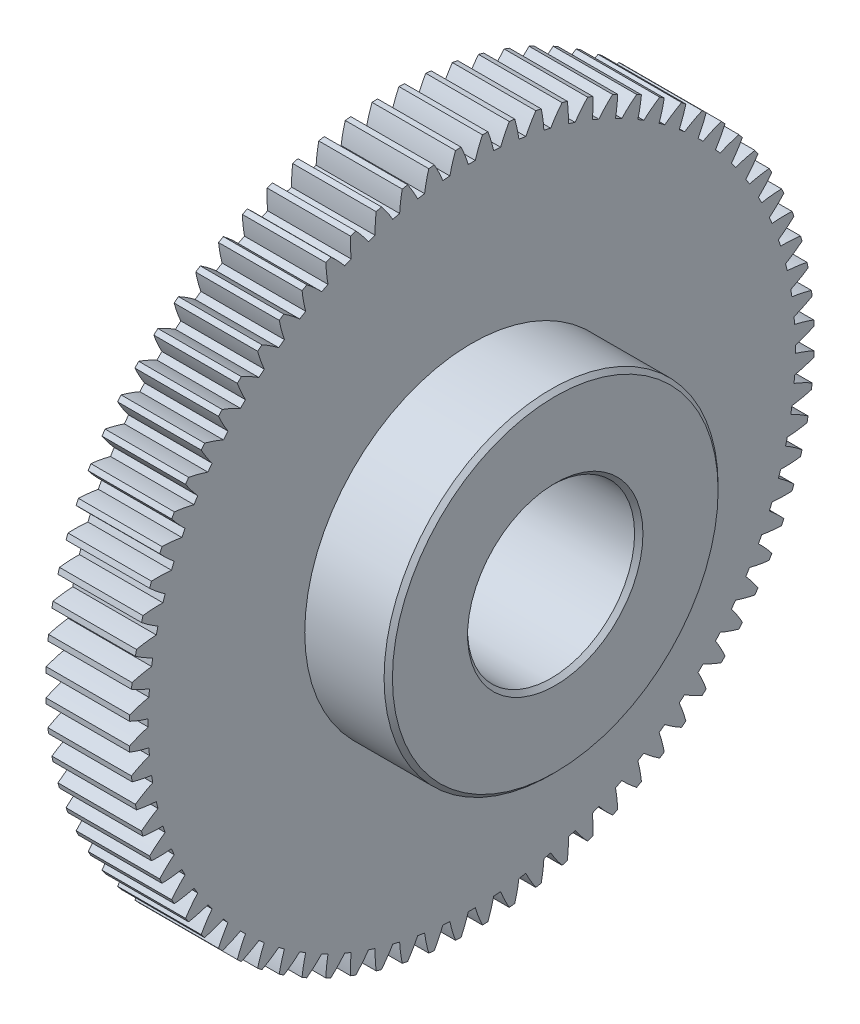
SolidWorks part; units mm, degrees
material "AISI 1045 鋼，冷拉"
ref_plane "Plane1" through (0, 0, 0) normal (0, 0, 1) x (1, 0, 0)
ref_plane "Plane2" through (0, 0, 0) normal (0, 1, 0) x (1, 0, 0)
ref_plane "Plane3" through (0, 0, 0) normal (1, 0, 0) x (0, 0, -1)
sketch "HoldingSke" plane through (0, 0, 0) normal (0, 1, 0) x (1, 0, 0)
  line L0 (0, 0) -> (0.1736, -0.9848)
  line L1 (-15, 0) -> (100, 0) construction
  line L2 (0, 0) -> (-2.1039, 2.3779)
  line L3 (0, 0) -> (-11.863, 4.5341)
  line L4 (0, 0) -> (1.4996, 8.5048)
  line L5 (0, 0) -> (-46.8476, -17.4728)
  line L6 (0, 0) -> (-8.2896, -5.593)
  line L7 (-2.1039, 2.3779) -> (8.6586, 51.2059)
  line L8 (-76.2, 54.61) -> (-76.1, 54.61)
  line L9 (-71.009, 38.7566) -> (-53.1078, 45.2721)
  line L10 (-76.2, 71.12) -> (104.1128, 71.12)
  line L11 (0, 0) -> (-10, 0)
  line L12 (-76.2, 101.6) -> (-76.162, 101.6)
  line L13 (24.9733, 27.94) -> (52.9518, 28.4284)
  line L14 (24.9733, 27.94) -> (24.9743, 27.94)
  line L15 (24.9733, 27.94) -> (100.4006, 29.5858)
  line L16 (-63.627, -1) -> (-12.827, -1)
  circle A0 centre (0, 0) radius 0.4
  circle A1 centre (0, 0) radius 37.5
  circle A2 centre (0, 0) radius 37.5
  circle A3 centre (0, 0) radius 0.4
  dimension "MHD" = 75
  dimension "Hub_dia" = 75
  dimension "Bore" = 0.8
  dimension "MBD" = 0.8
  dimension "Num_teeth" = 80
  dimension "Pitch" = 1
  dimension "Overall_len" = 50
  dimension "Show_teeth" = 80
  dimension "Thickness" = 10
  dimension "OAL" = 50.0001
  dimension "T_dim" = 0.1
  dimension "Ap" = 20
  dimension "H" = 19.05
  dimension "Pitch_radius" = 180.3128
  dimension "Width" = 10
  dimension "Backlash" = 0.038
  dimension "Addendum_fac" = 1
  dimension "Dedendum_fac" = 1.25
  dimension "Clearance_fac" = 0.25
  dimension "Dedendum_add" = 0.001
  dimension "Module" = 1
sketch "BasProSke" plane through (0, 0, 0) normal (0, 1, 0) x (1, 0, 0)
  line L0 (-10, 0) -> (60, 0) construction
  line L1 (0, 0) -> (0, 41)
  line L2 (0, 0) -> (10, 0)
  line L3 (10, 0) -> (10, 41)
  line L4 (10, 41) -> (0, 41)
  dimension "Thickness" = 10
  dimension "Diameter" = 82
revolve "Base-Revolve" add sketch "BasProSke" angle 360 about L0
sketch "TooCutSke" plane through (0, 0, 0) normal (1, 0, 0) x (0, 0, -1)
  line L1 (0, 0) -> (0, 107) construction
  line L2 (0, 0) -> (-0.8518, 39.9909) construction
  line L3 (0, 0) -> (-3.1403, 79.9254) construction
  line L4 (-0.8518, 39.9909) -> (-1.5701, 39.9627) construction
  arc A0 (0.4206, 38.7467) -> (-0.4206, 38.7467) centre (0, 0) ccw
  arc A1 (1.2919, 41.0051) -> (-1.2919, 41.0051) centre (0, 0) ccw
  circle A2 centre (0, 0) radius 40 construction
  circle A3 centre (0, 0) radius 37.5877 construction
  arc A4 (-0.4206, 38.7467) -> (-1.2919, 41.0051) centre (-15.7409, 34.133) ccw
  arc A5 (1.2919, 41.0051) -> (0.4206, 38.7467) centre (15.7409, 34.133) ccw
  dimension "Root_dia" = 77.498
  dimension "Overcut_dia" = 82.0508
  dimension "Pitch_dia" = 80
  dimension "Base_dia" = 75.1754
  dimension "Flank_rad" = 16
  dimension "Half_ang" = 2.25
  dimension "Half_CT" = 0.7188
extrude "ToothCut" cut sketch "TooCutSke" along normal through all
fillet "Breaks" [suppressed] radius 0.02
fillet "RootFillets" [suppressed] radius 0.251
pattern_circular "TeethCuts" count 80 every 4.5 about axis through (-10, 0, 0) along (1, 0, 0) of "ToothCut", "Breaks", "RootFillets"
sketch "HubNeaOneSke" plane through (0, 0, 0) normal (-1, 0, 0) x (0, 0, 1)
  circle A0 centre (0, 0) radius 37.5
  dimension "Diameter" = 75
extrude "HubNearOne" [suppressed] add sketch "HubNeaOneSke" along normal blind 40.0001
sketch "HubNeaBotSke" plane through (0, 0, 0) normal (-1, 0, 0) x (0, 0, 1)
  circle A0 centre (0, 0) radius 37.5
  dimension "Diameter" = 75
extrude "HubNearBoth" [suppressed] add sketch "HubNeaBotSke" along normal blind 20
ref_plane "FarPln" through (10, 0, 0) normal (1, 0, 0) x (0, 0, -1)
sketch "HubFarSke" plane through (10, 0, 0) normal (1, 0, 0) x (0, 0, -1)
  circle A0 centre (0, 0) radius 37.5
  dimension "Diameter" = 75
extrude "HubFar" [suppressed] add sketch "HubFarSke" along normal blind 20
sketch "草圖1" plane through (10, 0, 0) normal (1, 0, 0) x (0, 0, -1)
  circle A0 centre (0, 0) radius 20
  dimension "D1" = 40
extrude "填料-伸長1" add sketch "草圖1" along normal blind 10
sketch "BorSke" plane through (0, 0, 0) normal (1, 0, 0) x (0, 0, -1)
  circle A0 centre (0, 0) radius 10
  dimension "Diameter" = 20
extrude "Bore" cut sketch "BorSke" along normal mid plane 100.0001
sketch "KeySke" plane through (0, 0, 0) normal (1, 0, 0) x (0, 0, -1)
  line L0 (-0.05, 0) -> (-0.05, 0.5)
  line L1 (-0.05, 0.5) -> (0.05, 0.5)
  line L2 (0.05, 0.5) -> (0.05, 0)
  line L3 (0, 0) -> (0, 34) construction
  line L4 (-0.05, 0) -> (0.05, 0)
  dimension "Offset" = 0.5
  dimension "Width" = 0.1
extrude "Keyway" [suppressed] cut sketch "KeySke" along normal mid plane 100.0001
pattern_circular "Keyway2" [suppressed] count 2 every 90 about axis through (-10, 0, 0) along (1, 0, 0)
chamfer "導角1" distance 0.5 angle 45 3 edges at (0, 0, -10) (20, 0, -10) (20, 0, -20)
equation "' \"Module@HoldingSke\" = 6.35"
equation "' \"Num_teeth@HoldingSke\" = 12"
equation "' \"Ap@HoldingSke\" =  20"
equation "' \"Ap@HoldingSke\" = 20"
equation "' \"Width@HoldingSke\" = 0.5 * 25.4"
equation "' \"Hub_dia@HoldingSke\"= 1 * 25.4"
equation "' \"Hub_dia@HoldingSke\" = 1 * 25.4"
equation "' \"Overall_len@HoldingSke\" = 1.0 * 25.4"
equation "' \"Bore@HoldingSke\" = 0.75 * 25.4"
equation "' \"T_dim@HoldingSke\" = 0.1 * 25.4"
equation "' \"Width@KeySke\" = 0.25 * 25.4"
equation "' \"Show_teeth@HoldingSke\" = 13"
equation "' \"Backlash@HoldingSke\" = 0.009 * 25.4"
equation "' \"Addendum_fac@HoldingSke\" = 1.0"
equation "' \"Dedendum_fac@HoldingSke\" = 1.25"
equation "' \"Dedendum_add@HoldingSke\" = 0.00005 * 25.4"
equation "' \"Clearance_fac@HoldingSke\" = 0.25"
equation "\"Pitch@HoldingSke\" = 1 / \"Module@HoldingSke\""
equation "\"Overcut_dia@TooCutSke\" = (\"Num_teeth@HoldingSke\" + 2 * \"Addendum_fac@HoldingSke\") / \"Pitch@HoldingSke\" + 0.002 * 25.4"
equation "\"Pitch_dia@TooCutSke\" = \"Num_teeth@HoldingSke\" / \"Pitch@HoldingSke\""
equation "\"Base_dia@TooCutSke\" = \"Num_teeth@HoldingSke\" / \"Pitch@HoldingSke\" * cos((\"Ap@HoldingSke\"  * 3.14159265 / 180))"
equation "\"Root_dia@TooCutSke\" = (\"Num_teeth@HoldingSke\" + 2) / \"Pitch@HoldingSke\" - 2 * (\"Addendum_fac@HoldingSke\" + \"Dedendum_fac@HoldingSke\") / \"Pitch@HoldingSke\" - \"Dedendum_add@HoldingSke\" * 2"
equation "\"Half_ang@TooCutSke\" = 180 / \"Num_teeth@HoldingSke\""
equation "\"Half_CT@TooCutSke\" = \"Num_teeth@HoldingSke\" / \"Pitch@HoldingSke\" * sin((3.14159265 / 2 / \"Num_teeth@HoldingSke\")) / 2 - 7 * \"Backlash@HoldingSke\" / 4"
equation "\"Flank_rad@TooCutSke\" = \"Num_teeth@HoldingSke\" / \"Pitch@HoldingSke\" / 5"
equation "\"Radius@RootFillets\" = \"Clearance_fac@HoldingSke\" / \"Pitch@HoldingSke\" + \"Dedendum_add@HoldingSke\""
equation "\"Break_rad@Breaks\" = 0.02 / \"Pitch@HoldingSke\""
equation "\"Thickness@HoldingSke\" = \"Width@HoldingSke\""
equation "\"OAL@HoldingSke\" = \"Thickness@HoldingSke\""
equation "\"MHD@HoldingSke\" = (\"Num_teeth@HoldingSke\" + 2) / \"Pitch@HoldingSke\" - 2 * (\"Addendum_fac@HoldingSke\" + \"Dedendum_fac@HoldingSke\")  / \"Pitch@HoldingSke\" - \"Dedendum_add@HoldingSke\" * 2"
equation "\"MBD@HoldingSke\" = (\"Num_teeth@HoldingSke\" + 2) / \"Pitch@HoldingSke\" - 2 * (\"Addendum_fac@HoldingSke\" + \"Dedendum_fac@HoldingSke\")  / \"Pitch@HoldingSke\" - \"Dedendum_add@HoldingSke\" * 2 - 0.002 * 25.4"
equation "\"MHD@HoldingSke\" = ((sgn( \"MHD@HoldingSke\" - \"Hub_dia@HoldingSke\" )-1)*( \"MHD@HoldingSke\" - \"Hub_dia@HoldingSke\" ))/-2+ \"Hub_dia@HoldingSke\""
equation "\"MBD@HoldingSke\" = ((sgn( \"MBD@HoldingSke\" - \"Bore@HoldingSke\" )-1)*( \"MBD@HoldingSke\" - \"Bore@HoldingSke\" ))/-2+ \"Bore@HoldingSke\""
equation "\"OAL@HoldingSke\" = ((sgn( \"OAL@HoldingSke\" - \"Overall_len@HoldingSke\" )+1)*( \"OAL@HoldingSke\" - \"Overall_len@HoldingSke\" ))/2 + \"Overall_len@HoldingSke\" + 0.000002 * 25.4"
equation "\"Num_teeth@TeethCuts\" = int( \"Show_teeth@HoldingSke\" ) + 1"
equation "\"Num_teeth@TeethCuts\" = ((sgn( \"Num_teeth@TeethCuts\" - \"Num_teeth@HoldingSke\" )-1)*( \"Num_teeth@TeethCuts\" - \"Num_teeth@HoldingSke\" ))/-2+ \"Num_teeth@HoldingSke\""
equation "\"Num_teeth@TeethCuts\" = ((sgn( \"Num_teeth@TeethCuts\" - 2.0)+1)*( \"Num_teeth@TeethCuts\" - 2.0))/2 +2.0"
equation "\"Angle@TeethCuts\" = 360.0 / \"Num_teeth@HoldingSke\""
equation "\"Diameter@BasProSke\" = (\"Num_teeth@HoldingSke\" + 2 * \"Addendum_fac@HoldingSke\") / \"Pitch@HoldingSke\""
equation "\"Thickness@BasProSke\"  = \"Thickness@HoldingSke\""
equation "' \"Fillet_rad@BasProSke\" =  \"Thickness@HoldingSke\" * 0.05"
equation "' \"Fillet_rad@BasProSke\" = \"Thickness@HoldingSke\" * 0.05"
equation "\"MHD@HoldingSke\" = ((sgn( \"MHD@HoldingSke\" - \"Root_dia@TooCutSke\" )-1)*( \"MHD@HoldingSke\" - \"Root_dia@TooCutSke\" ))/-2+ \"Root_dia@TooCutSke\""
equation "\"Diameter@HubNeaOneSke\" = \"MHD@HoldingSke\""
equation "\"Length@HubNearOne\" = \"OAL@HoldingSke\" - \"Thickness@BasProSke\""
equation "\"Diameter@HubNeaBotSke\" = \"MHD@HoldingSke\""
equation "\"Length@HubNearBoth\" = ( \"OAL@HoldingSke\" - \"Thickness@BasProSke\" ) / 2.0"
equation "\"Thickness@FarPln\" = \"Thickness@BasProSke\""
equation "\"Diameter@HubFarSke\" = \"MHD@HoldingSke\""
equation "\"Length@HubFar\" = ( \"OAL@HoldingSke\" - \"Thickness@BasProSke\" ) / 2.0"
equation "\"D1@Bore\" = \"OAL@HoldingSke\" * 2.0"
equation "\"D1@Keyway\" = \"OAL@HoldingSke\" * 2.0"
equation "\"Offset@KeySke\" = \"T_dim@HoldingSke\" + \"MBD@HoldingSke\" / 2.0"
